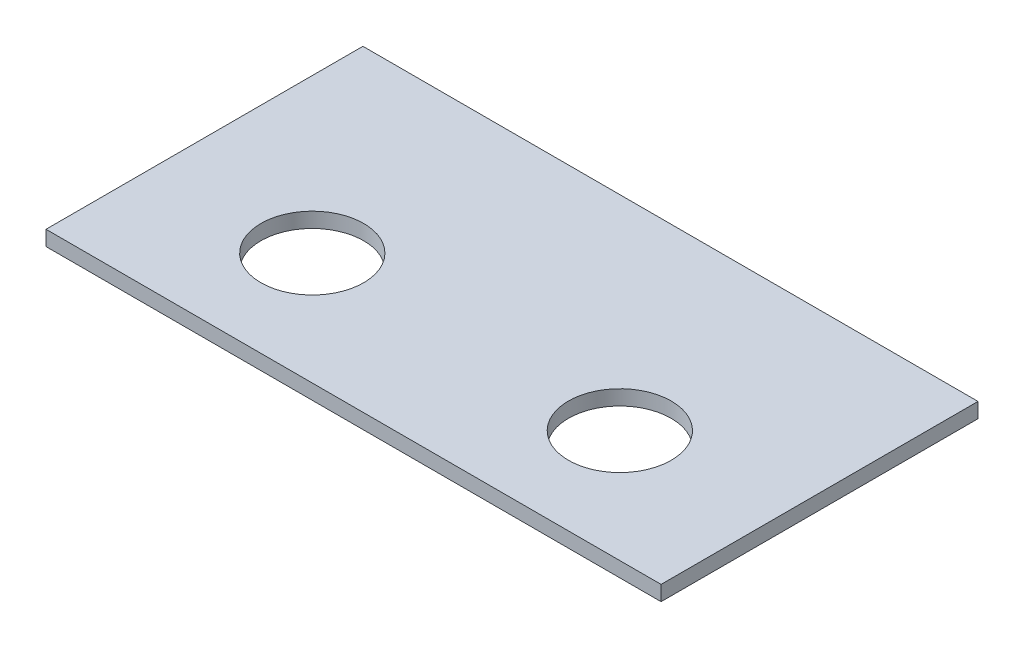
SolidWorks part; units mm, degrees
ref_plane "Front Plane" through (0, 0, 0) normal (0, 0, 1) x (1, 0, 0)
ref_plane "Top Plane" through (0, 0, 0) normal (0, 1, 0) x (1, 0, 0)
ref_plane "Right Plane" through (0, 0, 0) normal (1, 0, 0) x (0, 0, -1)
sketch "Sketch1" plane through (0, 0, 0) normal (0, 1, 0) x (1, 0, 0)
  line L0 (0, 42.25) -> (0, -42.25) construction
  line L1 (-82, 42.25) -> (82, 42.25)
  line L2 (-82, 42.25) -> (-82, -42.25)
  line L3 (-82, -42.25) -> (82, -42.25)
  line L4 (82, 42.25) -> (82, -42.25)
  line L5 (-82, 42.25) -> (82, -42.25) construction
  line L6 (-82, -42.25) -> (82, 42.25) construction
  line L7 (-82, 0) -> (0, 0) construction
  circle A0 centre (-41, -12.25) radius 13.7
  circle A1 centre (41, -12.25) radius 13.7
  point P0 (0, 0)
  point P14 (-41, 0)
  dimension "D3" = 27.4
  dimension "D1" = 164
  dimension "D2" = 84.5
  dimension "D4" = 30
extrude "Boss-Extrude1" add sketch "Sketch1" along normal blind 4
